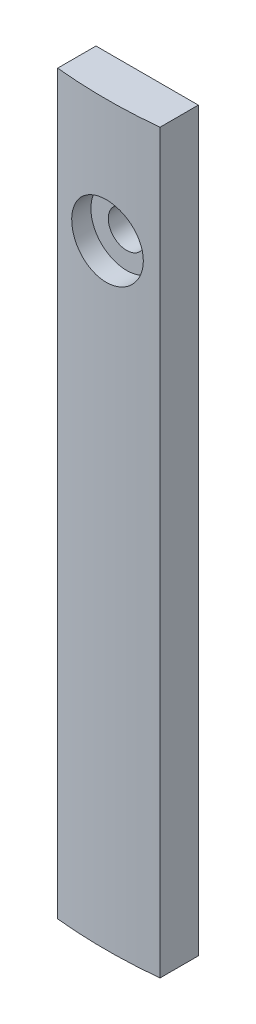
SolidWorks part; units mm, degrees
ref_plane "前视基准面" through (0, 0, 0) normal (0, 0, 1) x (1, 0, 0)
ref_plane "上视基准面" through (0, 0, 0) normal (0, 1, 0) x (1, 0, 0)
ref_plane "右视基准面" through (0, 0, 0) normal (1, 0, 0) x (0, 0, -1)
ref_plane "基准面4" through (0, 72, 0) normal (0, 1, 0) x (1, 0, 0)
sketch "草图1" plane through (0, 72, 0) normal (0, 1, 0) x (1, 0, 0)
  line L0 (1135, -1.4942) -> (1135, 2.25)
  line L1 (1135, 2.25) -> (1125, 2.25)
  line L2 (1125, 2.25) -> (1125, -1.4942)
  arc A0 (1125, -1.4942) -> (1135, -1.4942) centre (1130, 47.25) ccw
extrude "凸台-拉伸1" add sketch "草图1" against normal blind 72
hole_wizard "M3 六角头机械螺钉的柱形沉头孔1" positions "3D草图1" profile "草图2" counterbore size "M3" standard "ANSI Metric"
sketch3d "3D草图1"
  point P0 (1130, 60, 1.75)
  point P1 (1130, 7, 1.75)
sketch "草图2" plane through (1130, 60, 1.75) normal (1, 0, 0) x (0, -1, 0)
  line L0 (0, 0) -> (0, 4)
  line L1 (0, 4) -> (1.8, 4)
  line L3 (1.8, 4) -> (1.8, 2)
  line L4 (1.8, 2) -> (3.5, 2)
  line L5 (3.5, 2) -> (3.5, 0)
  line L7 (3.5, 0) -> (0, 0)
  line L11 (0, -6.35) -> (0, 107.95) construction
  dimension "通孔孔直径" = 3.6
  dimension "通孔孔深度" = 4
  dimension "柱形沉头孔直径" = 7
  dimension "柱形沉头孔深度" = 2
